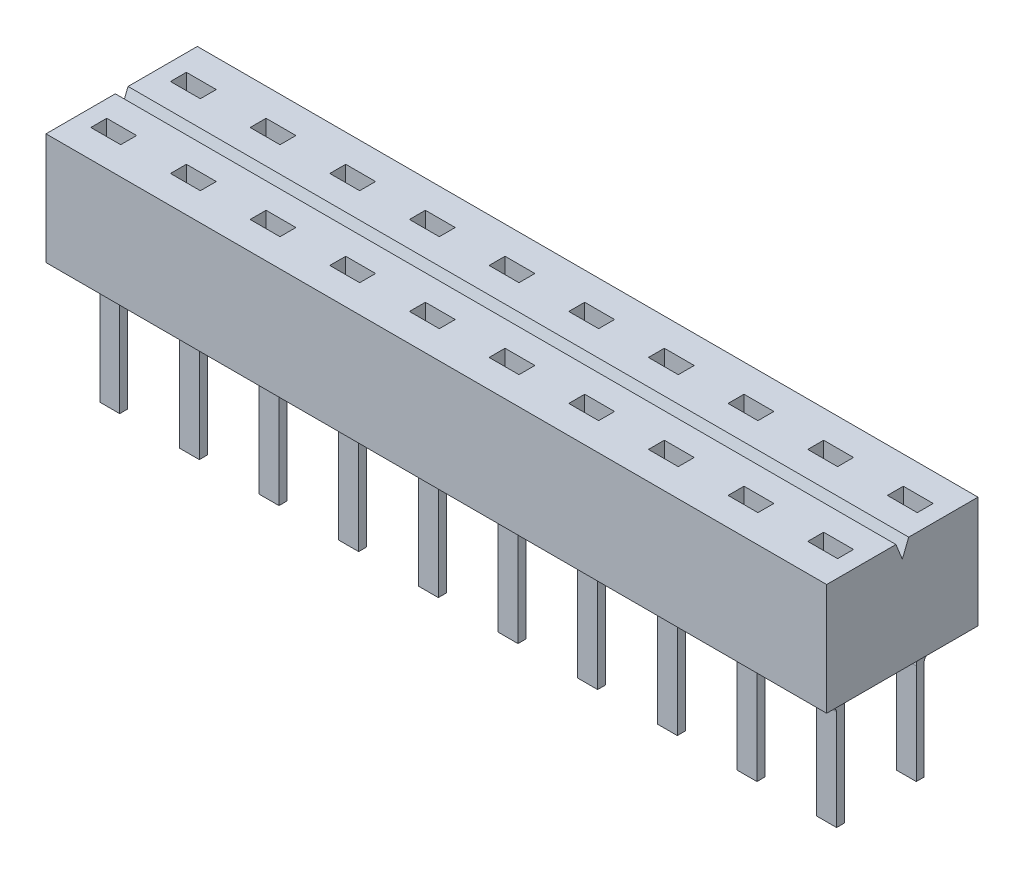
SolidWorks part; units mm, degrees
material "Pure Gold"
ref_plane "Front Plane" through (0, 0, 0) normal (0, 0, 1) x (1, 0, 0)
ref_plane "Top Plane" through (0, 0, 0) normal (0, 1, 0) x (1, 0, 0)
ref_plane "Right Plane" through (0, 0, 0) normal (1, 0, 0) x (0, 0, -1)
ref_plane "Plane1" through (0, 0.762, 0) normal (0, -1, 0) x (1, 0, 0)
sketch "Sketch1" plane through (0, 0.762, 0) normal (0, -1, 0) x (1, 0, 0)
  line L0 (-12.446, 2.413) -> (-12.446, -2.413)
  line L1 (-12.446, -2.413) -> (12.446, -2.413)
  line L2 (12.446, -2.413) -> (12.446, 2.413)
  line L3 (12.446, 2.413) -> (-12.446, 2.413)
extrude "Boss-Extrude1" add sketch "Sketch1" against normal blind 3.556
ref_plane "Plane2" through (8.5725, 0, 0) normal (-1, 0, 0) x (0, -1, 0)
sketch "Sketch2" plane through (8.5725, 0, 0) normal (-1, 0, 0) x (0, -1, 0)
  line L0 (0, 1.397) -> (-0.762, 2.286)
  line L1 (-0.762, 2.286) -> (-0.762, 1.8957)
  line L2 (-0.762, 1.8957) -> (-0.1168, 1.143)
  line L3 (-0.1168, 1.143) -> (3.2512, 1.143)
  line L4 (3.2512, 1.143) -> (3.2512, 1.397)
  line L5 (3.2512, 1.397) -> (0, 1.397)
extrude "Boss-Extrude2" add sketch "Sketch2" against normal blind 0.635
ref_plane "Plane3" through (6.0325, 0, 0) normal (-1, 0, 0) x (0, -1, 0)
sketch "Sketch3" plane through (6.0325, 0, 0) normal (-1, 0, 0) x (0, -1, 0)
  line L0 (0, 1.397) -> (-0.762, 2.286)
  line L1 (-0.762, 2.286) -> (-0.762, 1.8957)
  line L2 (-0.762, 1.8957) -> (-0.1168, 1.143)
  line L3 (-0.1168, 1.143) -> (3.2512, 1.143)
  line L4 (3.2512, 1.143) -> (3.2512, 1.397)
  line L5 (3.2512, 1.397) -> (0, 1.397)
extrude "Boss-Extrude3" add sketch "Sketch3" against normal blind 0.635
ref_plane "Plane4" through (3.4925, 0, 0) normal (-1, 0, 0) x (0, -1, 0)
sketch "Sketch4" plane through (3.4925, 0, 0) normal (-1, 0, 0) x (0, -1, 0)
  line L0 (0, 1.397) -> (-0.762, 2.286)
  line L1 (-0.762, 2.286) -> (-0.762, 1.8957)
  line L2 (-0.762, 1.8957) -> (-0.1168, 1.143)
  line L3 (-0.1168, 1.143) -> (3.2512, 1.143)
  line L4 (3.2512, 1.143) -> (3.2512, 1.397)
  line L5 (3.2512, 1.397) -> (0, 1.397)
extrude "Boss-Extrude4" add sketch "Sketch4" against normal blind 0.635
ref_plane "Plane5" through (0.9525, 0, 0) normal (-1, 0, 0) x (0, -1, 0)
sketch "Sketch5" plane through (0.9525, 0, 0) normal (-1, 0, 0) x (0, -1, 0)
  line L0 (0, 1.397) -> (-0.762, 2.286)
  line L1 (-0.762, 2.286) -> (-0.762, 1.8957)
  line L2 (-0.762, 1.8957) -> (-0.1168, 1.143)
  line L3 (-0.1168, 1.143) -> (3.2512, 1.143)
  line L4 (3.2512, 1.143) -> (3.2512, 1.397)
  line L5 (3.2512, 1.397) -> (0, 1.397)
extrude "Boss-Extrude5" add sketch "Sketch5" against normal blind 0.635
ref_plane "Plane6" through (-1.5875, 0, 0) normal (-1, 0, 0) x (0, -1, 0)
sketch "Sketch6" plane through (-1.5875, 0, 0) normal (-1, 0, 0) x (0, -1, 0)
  line L0 (0, 1.397) -> (-0.762, 2.286)
  line L1 (-0.762, 2.286) -> (-0.762, 1.8957)
  line L2 (-0.762, 1.8957) -> (-0.1168, 1.143)
  line L3 (-0.1168, 1.143) -> (3.2512, 1.143)
  line L4 (3.2512, 1.143) -> (3.2512, 1.397)
  line L5 (3.2512, 1.397) -> (0, 1.397)
extrude "Boss-Extrude6" add sketch "Sketch6" against normal blind 0.635
ref_plane "Plane7" through (-4.1275, 0, 0) normal (-1, 0, 0) x (0, -1, 0)
sketch "Sketch7" plane through (-4.1275, 0, 0) normal (-1, 0, 0) x (0, -1, 0)
  line L0 (0, 1.397) -> (-0.762, 2.286)
  line L1 (-0.762, 2.286) -> (-0.762, 1.8957)
  line L2 (-0.762, 1.8957) -> (-0.1168, 1.143)
  line L3 (-0.1168, 1.143) -> (3.2512, 1.143)
  line L4 (3.2512, 1.143) -> (3.2512, 1.397)
  line L5 (3.2512, 1.397) -> (0, 1.397)
extrude "Boss-Extrude7" add sketch "Sketch7" against normal blind 0.635
ref_plane "Plane8" through (-6.6675, 0, 0) normal (-1, 0, 0) x (0, -1, 0)
sketch "Sketch8" plane through (-6.6675, 0, 0) normal (-1, 0, 0) x (0, -1, 0)
  line L0 (0, 1.397) -> (-0.762, 2.286)
  line L1 (-0.762, 2.286) -> (-0.762, 1.8957)
  line L2 (-0.762, 1.8957) -> (-0.1168, 1.143)
  line L3 (-0.1168, 1.143) -> (3.2512, 1.143)
  line L4 (3.2512, 1.143) -> (3.2512, 1.397)
  line L5 (3.2512, 1.397) -> (0, 1.397)
extrude "Boss-Extrude8" add sketch "Sketch8" against normal blind 0.635
ref_plane "Plane9" through (-9.2075, 0, 0) normal (-1, 0, 0) x (0, -1, 0)
sketch "Sketch9" plane through (-9.2075, 0, 0) normal (-1, 0, 0) x (0, -1, 0)
  line L0 (0, 1.397) -> (-0.762, 2.286)
  line L1 (-0.762, 2.286) -> (-0.762, 1.8957)
  line L2 (-0.762, 1.8957) -> (-0.1168, 1.143)
  line L3 (-0.1168, 1.143) -> (3.2512, 1.143)
  line L4 (3.2512, 1.143) -> (3.2512, 1.397)
  line L5 (3.2512, 1.397) -> (0, 1.397)
extrude "Boss-Extrude9" add sketch "Sketch9" against normal blind 0.635
ref_plane "Plane10" through (-11.7475, 0, 0) normal (-1, 0, 0) x (0, -1, 0)
sketch "Sketch10" plane through (-11.7475, 0, 0) normal (-1, 0, 0) x (0, -1, 0)
  line L0 (0, 1.397) -> (-0.762, 2.286)
  line L1 (-0.762, 2.286) -> (-0.762, 1.8957)
  line L2 (-0.762, 1.8957) -> (-0.1168, 1.143)
  line L3 (-0.1168, 1.143) -> (3.2512, 1.143)
  line L4 (3.2512, 1.143) -> (3.2512, 1.397)
  line L5 (3.2512, 1.397) -> (0, 1.397)
extrude "Boss-Extrude10" add sketch "Sketch10" against normal blind 0.635
ref_plane "Plane11" through (11.1125, 0, 0) normal (-1, 0, 0) x (0, -1, 0)
sketch "Sketch11" plane through (11.1125, 0, 0) normal (-1, 0, 0) x (0, -1, 0)
  line L0 (-0.1168, -1.143) -> (-0.762, -1.8957)
  line L1 (-0.762, -1.8957) -> (-0.762, -2.286)
  line L2 (-0.762, -2.286) -> (0, -1.397)
  line L3 (0, -1.397) -> (3.2512, -1.397)
  line L4 (3.2512, -1.397) -> (3.2512, -1.143)
  line L5 (3.2512, -1.143) -> (-0.1168, -1.143)
extrude "Boss-Extrude11" add sketch "Sketch11" against normal blind 0.635
sketch "Sketch12" plane through (8.5725, 0, 0) normal (-1, 0, 0) x (0, -1, 0)
  line L0 (-0.1168, -1.143) -> (-0.762, -1.8957)
  line L1 (-0.762, -1.8957) -> (-0.762, -2.286)
  line L2 (-0.762, -2.286) -> (0, -1.397)
  line L3 (0, -1.397) -> (3.2512, -1.397)
  line L4 (3.2512, -1.397) -> (3.2512, -1.143)
  line L5 (3.2512, -1.143) -> (-0.1168, -1.143)
extrude "Boss-Extrude12" add sketch "Sketch12" against normal blind 0.635
sketch "Sketch13" plane through (6.0325, 0, 0) normal (-1, 0, 0) x (0, -1, 0)
  line L0 (-0.1168, -1.143) -> (-0.762, -1.8957)
  line L1 (-0.762, -1.8957) -> (-0.762, -2.286)
  line L2 (-0.762, -2.286) -> (0, -1.397)
  line L3 (0, -1.397) -> (3.2512, -1.397)
  line L4 (3.2512, -1.397) -> (3.2512, -1.143)
  line L5 (3.2512, -1.143) -> (-0.1168, -1.143)
extrude "Boss-Extrude13" add sketch "Sketch13" against normal blind 0.635
sketch "Sketch14" plane through (3.4925, 0, 0) normal (-1, 0, 0) x (0, -1, 0)
  line L0 (-0.1168, -1.143) -> (-0.762, -1.8957)
  line L1 (-0.762, -1.8957) -> (-0.762, -2.286)
  line L2 (-0.762, -2.286) -> (0, -1.397)
  line L3 (0, -1.397) -> (3.2512, -1.397)
  line L4 (3.2512, -1.397) -> (3.2512, -1.143)
  line L5 (3.2512, -1.143) -> (-0.1168, -1.143)
extrude "Boss-Extrude14" add sketch "Sketch14" against normal blind 0.635
sketch "Sketch15" plane through (0.9525, 0, 0) normal (-1, 0, 0) x (0, -1, 0)
  line L0 (-0.1168, -1.143) -> (-0.762, -1.8957)
  line L1 (-0.762, -1.8957) -> (-0.762, -2.286)
  line L2 (-0.762, -2.286) -> (0, -1.397)
  line L3 (0, -1.397) -> (3.2512, -1.397)
  line L4 (3.2512, -1.397) -> (3.2512, -1.143)
  line L5 (3.2512, -1.143) -> (-0.1168, -1.143)
extrude "Boss-Extrude15" add sketch "Sketch15" against normal blind 0.635
sketch "Sketch16" plane through (-1.5875, 0, 0) normal (-1, 0, 0) x (0, -1, 0)
  line L0 (-0.1168, -1.143) -> (-0.762, -1.8957)
  line L1 (-0.762, -1.8957) -> (-0.762, -2.286)
  line L2 (-0.762, -2.286) -> (0, -1.397)
  line L3 (0, -1.397) -> (3.2512, -1.397)
  line L4 (3.2512, -1.397) -> (3.2512, -1.143)
  line L5 (3.2512, -1.143) -> (-0.1168, -1.143)
extrude "Boss-Extrude16" add sketch "Sketch16" against normal blind 0.635
sketch "Sketch17" plane through (-4.1275, 0, 0) normal (-1, 0, 0) x (0, -1, 0)
  line L0 (-0.1168, -1.143) -> (-0.762, -1.8957)
  line L1 (-0.762, -1.8957) -> (-0.762, -2.286)
  line L2 (-0.762, -2.286) -> (0, -1.397)
  line L3 (0, -1.397) -> (3.2512, -1.397)
  line L4 (3.2512, -1.397) -> (3.2512, -1.143)
  line L5 (3.2512, -1.143) -> (-0.1168, -1.143)
extrude "Boss-Extrude17" add sketch "Sketch17" against normal blind 0.635
sketch "Sketch18" plane through (-6.6675, 0, 0) normal (-1, 0, 0) x (0, -1, 0)
  line L0 (-0.1168, -1.143) -> (-0.762, -1.8957)
  line L1 (-0.762, -1.8957) -> (-0.762, -2.286)
  line L2 (-0.762, -2.286) -> (0, -1.397)
  line L3 (0, -1.397) -> (3.2512, -1.397)
  line L4 (3.2512, -1.397) -> (3.2512, -1.143)
  line L5 (3.2512, -1.143) -> (-0.1168, -1.143)
extrude "Boss-Extrude18" add sketch "Sketch18" against normal blind 0.635
sketch "Sketch19" plane through (-9.2075, 0, 0) normal (-1, 0, 0) x (0, -1, 0)
  line L0 (-0.1168, -1.143) -> (-0.762, -1.8957)
  line L1 (-0.762, -1.8957) -> (-0.762, -2.286)
  line L2 (-0.762, -2.286) -> (0, -1.397)
  line L3 (0, -1.397) -> (3.2512, -1.397)
  line L4 (3.2512, -1.397) -> (3.2512, -1.143)
  line L5 (3.2512, -1.143) -> (-0.1168, -1.143)
extrude "Boss-Extrude19" add sketch "Sketch19" against normal blind 0.635
sketch "Sketch20" plane through (-11.7475, 0, 0) normal (-1, 0, 0) x (0, -1, 0)
  line L0 (-0.1168, -1.143) -> (-0.762, -1.8957)
  line L1 (-0.762, -1.8957) -> (-0.762, -2.286)
  line L2 (-0.762, -2.286) -> (0, -1.397)
  line L3 (0, -1.397) -> (3.2512, -1.397)
  line L4 (3.2512, -1.397) -> (3.2512, -1.143)
  line L5 (3.2512, -1.143) -> (-0.1168, -1.143)
extrude "Boss-Extrude20" add sketch "Sketch20" against normal blind 0.635
sketch "Sketch21" plane through (11.1125, 0, 0) normal (-1, 0, 0) x (0, -1, 0)
  line L0 (0, 1.397) -> (-0.762, 2.286)
  line L1 (-0.762, 2.286) -> (-0.762, 1.8957)
  line L2 (-0.762, 1.8957) -> (-0.1168, 1.143)
  line L3 (-0.1168, 1.143) -> (3.2512, 1.143)
  line L4 (3.2512, 1.143) -> (3.2512, 1.397)
  line L5 (3.2512, 1.397) -> (0, 1.397)
extrude "Boss-Extrude21" add sketch "Sketch21" against normal blind 0.635
fillet "Fillet1" radius 0.127 20 edges at (-1.27, 0, -1.397) (-11.43, 0, -1.397) (-11.43, 0, 1.397) (1.27, 0, -1.397) (8.89, 0, -1.397) (-8.89, 0, 1.397) (-6.35, 0, -1.397) (-8.89, 0, -1.397) (1.27, 0, 1.397) (-6.35, 0, 1.397) (3.81, 0, 1.397) (3.81, 0, -1.397) (6.35, 0, 1.397) (-3.81, 0, 1.397) (8.89, 0, 1.397) (-3.81, 0, -1.397) (11.43, 0, 1.397) (-1.27, 0, 1.397) (6.35, 0, -1.397) (11.43, 0, -1.397)
fillet "Fillet2" radius 0.381 20 edges at (-1.27, 0.1168, 1.143) (-11.43, 0.1168, 1.143) (8.89, 0.1168, 1.143) (-8.89, 0.1168, -1.143) (-6.35, 0.1168, 1.143) (-6.35, 0.1168, -1.143) (3.81, 0.1168, 1.143) (-3.81, 0.1168, -1.143) (11.43, 0.1168, 1.143) (-1.27, 0.1168, -1.143) (-8.89, 0.1168, 1.143) (1.27, 0.1168, -1.143) (-3.81, 0.1168, 1.143) (3.81, 0.1168, -1.143) (1.27, 0.1168, 1.143) (6.35, 0.1168, -1.143) (6.35, 0.1168, 1.143) (8.89, 0.1168, -1.143) (11.43, 0.1168, -1.143) (-11.43, 0.1168, -1.143)
sketch "Sketch22" plane through (0, 4.318, 0) normal (0, 1, 0) x (-1, 0, 0)
  line L0 (10.9537, 1.016) -> (11.9062, 1.016)
  line L1 (11.9062, 1.016) -> (11.9062, 1.524)
  line L2 (11.9062, 1.524) -> (10.9537, 1.524)
  line L3 (10.9537, 1.524) -> (10.9537, 1.016)
extrude "Cut-Extrude1" cut sketch "Sketch22" against normal blind 3.302
sketch "Sketch23" plane through (0, 4.318, 0) normal (0, 1, 0) x (-1, 0, 0)
  line L0 (8.4137, 1.016) -> (9.3663, 1.016)
  line L1 (9.3663, 1.016) -> (9.3663, 1.524)
  line L2 (9.3663, 1.524) -> (8.4137, 1.524)
  line L3 (8.4137, 1.524) -> (8.4137, 1.016)
extrude "Cut-Extrude2" cut sketch "Sketch23" against normal blind 3.302
sketch "Sketch24" plane through (0, 4.318, 0) normal (0, 1, 0) x (-1, 0, 0)
  line L0 (-9.3663, 1.016) -> (-8.4137, 1.016)
  line L1 (-8.4137, 1.016) -> (-8.4137, 1.524)
  line L2 (-8.4137, 1.524) -> (-9.3663, 1.524)
  line L3 (-9.3663, 1.524) -> (-9.3663, 1.016)
extrude "Cut-Extrude3" cut sketch "Sketch24" against normal blind 3.302
sketch "Sketch25" plane through (0, 4.318, 0) normal (0, 1, 0) x (-1, 0, 0)
  line L0 (-6.8262, 1.016) -> (-5.8738, 1.016)
  line L1 (-5.8738, 1.016) -> (-5.8738, 1.524)
  line L2 (-5.8738, 1.524) -> (-6.8262, 1.524)
  line L3 (-6.8262, 1.524) -> (-6.8262, 1.016)
extrude "Cut-Extrude4" cut sketch "Sketch25" against normal blind 3.302
sketch "Sketch26" plane through (0, 4.318, 0) normal (0, 1, 0) x (-1, 0, 0)
  line L0 (-4.2862, 1.016) -> (-3.3337, 1.016)
  line L1 (-3.3337, 1.016) -> (-3.3337, 1.524)
  line L2 (-3.3337, 1.524) -> (-4.2862, 1.524)
  line L3 (-4.2862, 1.524) -> (-4.2862, 1.016)
extrude "Cut-Extrude5" cut sketch "Sketch26" against normal blind 3.302
sketch "Sketch27" plane through (0, 4.318, 0) normal (0, 1, 0) x (-1, 0, 0)
  line L0 (-1.7463, 1.016) -> (-0.7937, 1.016)
  line L1 (-0.7937, 1.016) -> (-0.7937, 1.524)
  line L2 (-0.7937, 1.524) -> (-1.7463, 1.524)
  line L3 (-1.7463, 1.524) -> (-1.7463, 1.016)
extrude "Cut-Extrude6" cut sketch "Sketch27" against normal blind 3.302
sketch "Sketch28" plane through (0, 4.318, 0) normal (0, 1, 0) x (-1, 0, 0)
  line L0 (0.7937, 1.016) -> (1.7463, 1.016)
  line L1 (1.7463, 1.016) -> (1.7463, 1.524)
  line L2 (1.7463, 1.524) -> (0.7937, 1.524)
  line L3 (0.7937, 1.524) -> (0.7937, 1.016)
extrude "Cut-Extrude7" cut sketch "Sketch28" against normal blind 3.302
sketch "Sketch29" plane through (0, 4.318, 0) normal (0, 1, 0) x (-1, 0, 0)
  line L0 (3.3337, 1.016) -> (4.2862, 1.016)
  line L1 (4.2862, 1.016) -> (4.2862, 1.524)
  line L2 (4.2862, 1.524) -> (3.3337, 1.524)
  line L3 (3.3337, 1.524) -> (3.3337, 1.016)
extrude "Cut-Extrude8" cut sketch "Sketch29" against normal blind 3.302
sketch "Sketch30" plane through (0, 4.318, 0) normal (0, 1, 0) x (-1, 0, 0)
  line L0 (5.8738, 1.016) -> (6.8262, 1.016)
  line L1 (6.8262, 1.016) -> (6.8262, 1.524)
  line L2 (6.8262, 1.524) -> (5.8738, 1.524)
  line L3 (5.8738, 1.524) -> (5.8738, 1.016)
extrude "Cut-Extrude9" cut sketch "Sketch30" against normal blind 3.302
sketch "Sketch31" plane through (0, 4.318, 0) normal (0, 1, 0) x (-1, 0, 0)
  line L0 (-11.9062, -1.524) -> (-10.9537, -1.524)
  line L1 (-10.9537, -1.524) -> (-10.9537, -1.016)
  line L2 (-10.9537, -1.016) -> (-11.9062, -1.016)
  line L3 (-11.9062, -1.016) -> (-11.9062, -1.524)
extrude "Cut-Extrude10" cut sketch "Sketch31" against normal blind 3.302
sketch "Sketch32" plane through (0, 4.318, 0) normal (0, 1, 0) x (-1, 0, 0)
  line L0 (-9.3663, -1.524) -> (-8.4137, -1.524)
  line L1 (-8.4137, -1.524) -> (-8.4137, -1.016)
  line L2 (-8.4137, -1.016) -> (-9.3663, -1.016)
  line L3 (-9.3663, -1.016) -> (-9.3663, -1.524)
extrude "Cut-Extrude11" cut sketch "Sketch32" against normal blind 3.302
sketch "Sketch33" plane through (0, 4.318, 0) normal (0, 1, 0) x (-1, 0, 0)
  line L0 (-6.8262, -1.524) -> (-5.8738, -1.524)
  line L1 (-5.8738, -1.524) -> (-5.8738, -1.016)
  line L2 (-5.8738, -1.016) -> (-6.8262, -1.016)
  line L3 (-6.8262, -1.016) -> (-6.8262, -1.524)
extrude "Cut-Extrude12" cut sketch "Sketch33" against normal blind 3.302
sketch "Sketch34" plane through (0, 4.318, 0) normal (0, 1, 0) x (-1, 0, 0)
  line L0 (-4.2862, -1.524) -> (-3.3337, -1.524)
  line L1 (-3.3337, -1.524) -> (-3.3337, -1.016)
  line L2 (-3.3337, -1.016) -> (-4.2862, -1.016)
  line L3 (-4.2862, -1.016) -> (-4.2862, -1.524)
extrude "Cut-Extrude13" cut sketch "Sketch34" against normal blind 3.302
sketch "Sketch35" plane through (0, 4.318, 0) normal (0, 1, 0) x (-1, 0, 0)
  line L0 (-1.7463, -1.524) -> (-0.7937, -1.524)
  line L1 (-0.7937, -1.524) -> (-0.7937, -1.016)
  line L2 (-0.7937, -1.016) -> (-1.7463, -1.016)
  line L3 (-1.7463, -1.016) -> (-1.7463, -1.524)
extrude "Cut-Extrude14" cut sketch "Sketch35" against normal blind 3.302
sketch "Sketch36" plane through (0, 4.318, 0) normal (0, 1, 0) x (-1, 0, 0)
  line L0 (0.7937, -1.524) -> (1.7463, -1.524)
  line L1 (1.7463, -1.524) -> (1.7463, -1.016)
  line L2 (1.7463, -1.016) -> (0.7937, -1.016)
  line L3 (0.7937, -1.016) -> (0.7937, -1.524)
extrude "Cut-Extrude15" cut sketch "Sketch36" against normal blind 3.302
sketch "Sketch37" plane through (0, 4.318, 0) normal (0, 1, 0) x (-1, 0, 0)
  line L0 (3.3337, -1.524) -> (4.2862, -1.524)
  line L1 (4.2862, -1.524) -> (4.2862, -1.016)
  line L2 (4.2862, -1.016) -> (3.3337, -1.016)
  line L3 (3.3337, -1.016) -> (3.3337, -1.524)
extrude "Cut-Extrude16" cut sketch "Sketch37" against normal blind 3.302
sketch "Sketch38" plane through (0, 4.318, 0) normal (0, 1, 0) x (-1, 0, 0)
  line L0 (5.8738, -1.524) -> (6.8262, -1.524)
  line L1 (6.8262, -1.524) -> (6.8262, -1.016)
  line L2 (6.8262, -1.016) -> (5.8738, -1.016)
  line L3 (5.8738, -1.016) -> (5.8738, -1.524)
extrude "Cut-Extrude17" cut sketch "Sketch38" against normal blind 3.302
sketch "Sketch39" plane through (0, 4.318, 0) normal (0, 1, 0) x (-1, 0, 0)
  line L0 (8.4137, -1.524) -> (9.3663, -1.524)
  line L1 (9.3663, -1.524) -> (9.3663, -1.016)
  line L2 (9.3663, -1.016) -> (8.4137, -1.016)
  line L3 (8.4137, -1.016) -> (8.4137, -1.524)
extrude "Cut-Extrude18" cut sketch "Sketch39" against normal blind 3.302
sketch "Sketch40" plane through (0, 4.318, 0) normal (0, 1, 0) x (-1, 0, 0)
  line L0 (10.9537, -1.524) -> (11.9062, -1.524)
  line L1 (11.9062, -1.524) -> (11.9062, -1.016)
  line L2 (11.9062, -1.016) -> (10.9537, -1.016)
  line L3 (10.9537, -1.016) -> (10.9537, -1.524)
extrude "Cut-Extrude19" cut sketch "Sketch40" against normal blind 3.302
sketch "Sketch41" plane through (0, 4.318, 0) normal (0, 1, 0) x (-1, 0, 0)
  line L0 (-11.9062, 1.016) -> (-10.9537, 1.016)
  line L1 (-10.9537, 1.016) -> (-10.9537, 1.524)
  line L2 (-10.9537, 1.524) -> (-11.9062, 1.524)
  line L3 (-11.9062, 1.524) -> (-11.9062, 1.016)
extrude "Cut-Extrude20" cut sketch "Sketch41" against normal blind 3.302
sketch "Sketch42" plane through (-12.446, 0, 0) normal (-1, 0, 0) x (0, 0, 1)
  line L0 (-0.2032, 4.318) -> (0, 3.81)
  line L1 (0, 3.81) -> (0.2032, 4.318)
  line L2 (0.2032, 4.318) -> (-0.2032, 4.318)
extrude "Cut-Extrude21" cut sketch "Sketch42" against normal through all
ref_plane "Plane12" through (11.43, 0, 0) normal (1, 0, 0) x (0, 0, -1)
sketch "Sketch43" plane through (11.43, 0, 0) normal (1, 0, 0) x (0, 0, -1)
  line L0 (-1.143, -3.2512) -> (-1.397, -3.2512) construction
  line L1 (-1.143, -3.2512) -> (-1.397, -3.2512) construction
  line L2 (-1.27, -1003.2512) -> (-1.27, 48996.7488) construction
  point P5 (-1.27, -3.2512)
